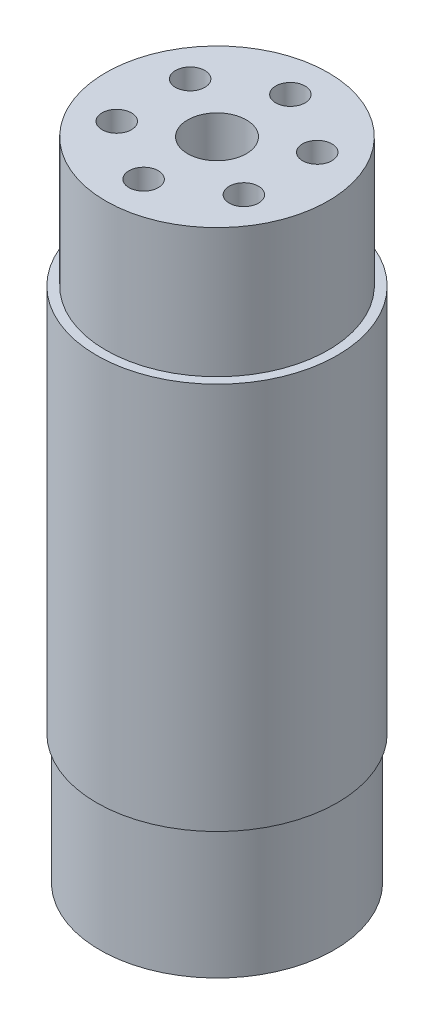
SolidWorks part; units mm, degrees
material "ABS"
ref_plane "Plan de face" through (0, 0, 0) normal (0, 0, 1) x (1, 0, 0)
ref_plane "Plan de dessus" through (0, 0, 0) normal (0, 1, 0) x (1, 0, 0)
ref_plane "Plan de droite" through (0, 0, 0) normal (1, 0, 0) x (0, 0, -1)
sketch "Esquisse1" plane through (0, 0, 0) normal (0, 1, 0) x (1, 0, 0)
  circle A0 centre (0, 0) radius 20.5
  dimension "D1" = 41
extrude "Boss.-Extru.1" add sketch "Esquisse1" along normal blind 110
sketch "Esquisse2" plane through (0, 110, 0) normal (0, 1, 0) x (1, 0, 0)
  circle A0 centre (0, 0) radius 18.95
  dimension "D1" = 37.9
extrude "Enlèv. mat.-Extru.1" cut sketch "Esquisse2" against normal blind 22 flip side to cut
sketch "Esquisse3" plane through (0, 0, 0) normal (0, -1, 0) x (1, 0, 0)
  circle A0 centre (0, 0) radius 19.95
  dimension "D1" = 39.9
extrude "Enlèv. mat.-Extru.2" cut sketch "Esquisse3" against normal blind 22 flip side to cut
sketch "Esquisse5" plane through (0, 110, 0) normal (0, 1, 0) x (1, 0, 0)
  circle A0 centre (0, 0) radius 5
  dimension "D1" = 10
extrude "Enlèv. mat.-Extru.3" cut sketch "Esquisse5" against normal through all
sketch "Esquisse6" plane through (0, 110, 0) normal (0, 1, 0) x (1, 0, 0)
  circle A0 centre (0, 0) radius 12.5 construction
  circle A1 centre (0, -12.5) radius 2.5
  circle A2 centre (-10.8253, -6.25) radius 2.5
  circle A3 centre (-10.8253, 6.25) radius 2.5
  circle A4 centre (0, 12.5) radius 2.5
  circle A5 centre (10.8253, 6.25) radius 2.5
  circle A6 centre (10.8253, -6.25) radius 2.5
  dimension "D1" = 5
  dimension "D2" = 25
  dimension "D3" = 6
extrude "Enlèv. mat.-Extru.4" cut sketch "Esquisse6" against normal blind 50
sketch "Esquisse7" plane through (0, 0, 0) normal (0, -1, 0) x (1, 0, 0)
  circle A1 centre (10.8253, -6.25) radius 2.5
  circle A2 centre (10.8253, -6.25) radius 2.5
  circle A3 centre (0, -12.5) radius 2.5
  circle A4 centre (0, -12.5) radius 2.5
  circle A5 centre (-10.8253, -6.25) radius 2.5
  circle A6 centre (-10.8253, -6.25) radius 2.5
  circle A7 centre (-10.8253, 6.25) radius 2.5
  circle A8 centre (-10.8253, 6.25) radius 2.5
  circle A9 centre (0, 12.5) radius 2.5
  circle A10 centre (0, 12.5) radius 2.5
  circle A11 centre (10.8253, 6.25) radius 2.5
  circle A12 centre (10.8253, 6.25) radius 2.5
  dimension "D1" = 0
  dimension "D2" = 0
  dimension "D3" = 0
  dimension "D4" = 0
  dimension "D5" = 0
  dimension "D6" = 0
extrude "Enlèv. mat.-Extru.5" cut sketch "Esquisse7" against normal blind 50
